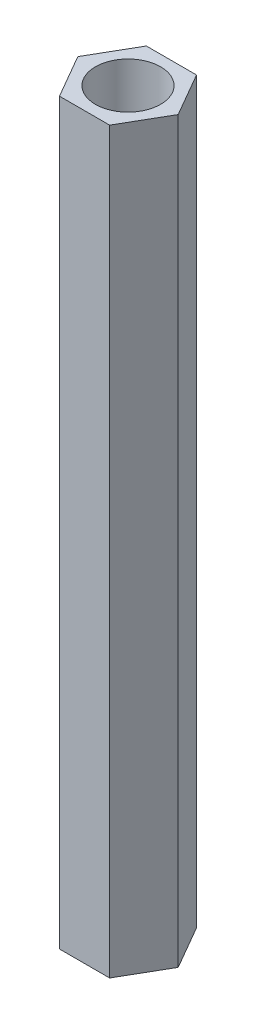
SolidWorks part; units mm, degrees
material "Commercial Bronze, UNS C22000 (90-10 Bronze)"
ref_plane "Alzado" through (0, 0, 0) normal (0, 0, 1) x (1, 0, 0)
ref_plane "Planta" through (0, 0, 0) normal (0, 1, 0) x (1, 0, 0)
ref_plane "Vista lateral" through (0, 0, 0) normal (1, 0, 0) x (0, 0, -1)
sketch "Croquis1" plane through (0, 0, 0) normal (0, 1, 0) x (1, 0, 0)
  line L1 (1.1547, 2) -> (-1.1547, 2)
  line L2 (-1.1547, 2) -> (-2.3094, 0)
  line L3 (-2.3094, 0) -> (-1.1547, -2)
  line L4 (-1.1547, -2) -> (1.1547, -2)
  line L5 (1.1547, -2) -> (2.3094, 0)
  line L6 (2.3094, 0) -> (1.1547, 2)
  circle A0 centre (0, 0) radius 2 construction
  circle A1 centre (0, 0) radius 1.5
  dimension "D1" = 4
  dimension "D2" = 3
extrude "Saliente-Extruir1" add sketch "Croquis1" along normal mid plane 34
